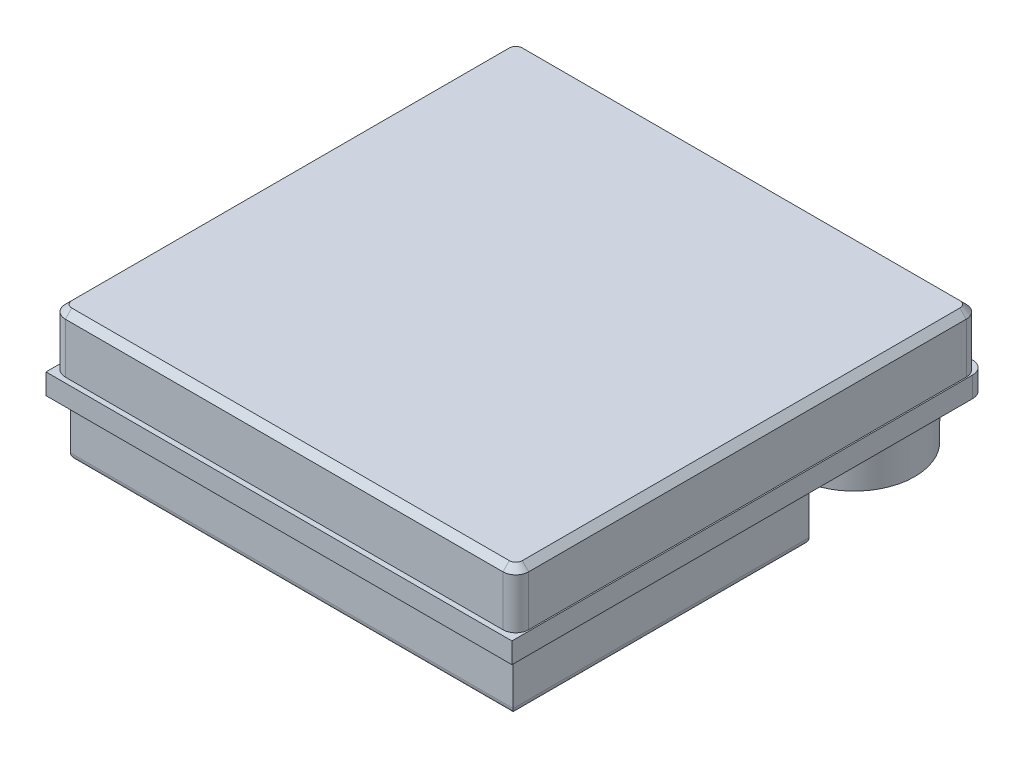
SolidWorks part; units mm, degrees
ref_plane "Front Plane" through (0, 0, 0) normal (0, 0, 1) x (1, 0, 0)
ref_plane "Top Plane" through (0, 0, 0) normal (0, 1, 0) x (1, 0, 0)
ref_plane "Right Plane" through (0, 0, 0) normal (1, 0, 0) x (0, 0, -1)
sketch "Sketch1" plane through (0, 0, 0) normal (0, 1, 0) x (1, 0, 0)
  line L1 (-9.05, 9.2) -> (9.05, 9.2)
  line L2 (-9.05, 9.2) -> (-9.05, -9.2)
  line L3 (-9.05, -9.2) -> (9.05, -9.2)
  line L4 (9.05, 9.2) -> (9.05, -9.2)
  line L5 (-9.05, 9.2) -> (9.05, -9.2) construction
  line L6 (-9.05, -9.2) -> (9.05, 9.2) construction
  point P0 (0, 0)
  dimension "D1" = 18.4
  dimension "D2" = 18.1
extrude "Boss-Extrude1" add sketch "Sketch1" along normal mid plane 0.8
sketch "Sketch2" plane through (0, 0.4, 0) normal (0, 1, 0) x (1, 0, 0)
  line L1 (9, 9) -> (-9, 9)
  line L2 (9, 9) -> (9, -9)
  line L3 (9, -9) -> (-9, -9)
  line L4 (-9, 9) -> (-9, -9)
  line L5 (9, 9) -> (-9, -9) construction
  line L6 (9, -9) -> (-9, 9) construction
  point P0 (0, 0)
  dimension "D1" = 18
extrude "Boss-Extrude2" add sketch "Sketch2" along normal blind 2.2
sketch "Sketch3" plane through (0, -0.4, 0) normal (0, -1, 0) x (1, 0, 0)
  line L0 (0, 9.2) -> (0, -9.2) construction
  line L1 (-9.05, 9.2) -> (9.05, 9.2) construction
  line L2 (9.05, -9.2) -> (-9.05, -9.2) construction
  line L4 (-3.075, -4.4) -> (3.075, -4.4)
  line L5 (-3.075, -4.4) -> (-3.075, -8.7)
  line L6 (-3.075, -8.7) -> (3.075, -8.7)
  line L7 (3.075, -4.4) -> (3.075, -8.7)
  line L8 (-3.075, -4.4) -> (3.075, -8.7) construction
  line L9 (-3.075, -8.7) -> (3.075, -4.4) construction
  point P6 (0, -6.55)
  dimension "D1" = 6.15
  dimension "D2" = 4.3
  dimension "D3" = 0.5
extrude "Boss-Extrude3" add sketch "Sketch3" along normal blind 3
sketch "Sketch4" plane through (0, 0, -8.7) normal (0, 0, -1) x (-1, 0, 0)
  line L8 (2.575, -0.9) -> (-2.575, -0.9)
  line L9 (-2.575, -0.9) -> (-2.575, -2.9)
  line L10 (-2.575, -2.9) -> (2.575, -2.9)
  line L11 (2.575, -2.9) -> (2.575, -0.9)
  line L12 (2.575, -0.9) -> (-2.575, -0.9)
  line L13 (-2.575, -0.9) -> (-2.575, -2.9)
  line L14 (-2.575, -2.9) -> (2.575, -2.9)
  line L15 (2.575, -2.9) -> (2.575, -0.9)
  dimension "D1" = 0.5
extrude "Cut-Extrude1" cut sketch "Sketch4" against normal blind 3.5
sketch "Sketch5" plane through (0, -0.4, 0) normal (0, -1, 0) x (1, 0, 0)
  line L0 (0, 9.2) -> (0, -9.2) construction
  line L1 (-9.05, 9.2) -> (9.05, 9.2) construction
  line L2 (9.05, -9.2) -> (-9.05, -9.2) construction
  line L4 (-8.6, 8.7) -> (8.6, 8.7)
  line L5 (-8.6, 8.7) -> (-8.6, -2.8)
  line L6 (-8.6, -2.8) -> (8.6, -2.8)
  line L7 (8.6, 8.7) -> (8.6, -2.8)
  line L8 (-8.6, 8.7) -> (8.6, -2.8) construction
  line L9 (-8.6, -2.8) -> (8.6, 8.7) construction
  point P6 (0, 2.95)
  dimension "D1" = 0.5
  dimension "D2" = 17.2
  dimension "D3" = 11.5
extrude "Boss-Extrude4" add sketch "Sketch5" along normal blind 2.2
fillet "Fillet1" radius 0.25 4 edges at (0, -2.6, -2.8) (-8.6, -2.6, 2.95) (0, -2.6, 8.7) (8.6, -2.6, 2.95)
sketch "Sketch6" plane through (0, -0.4, 0) normal (0, -1, 0) x (1, 0, 0)
  line L9 (8.85, -9) -> (8.85, 9)
  line L10 (8.85, 9) -> (-8.85, 9)
  line L11 (-8.85, 9) -> (-8.85, -9)
  line L12 (-8.85, -9) -> (8.85, -9)
  line L13 (8.85, -9) -> (8.85, 9)
  line L14 (8.85, 9) -> (-8.85, 9)
  line L15 (-8.85, 9) -> (-8.85, -9)
  line L16 (-8.85, -9) -> (8.85, -9)
  circle A0 centre (6.5, -6.65) radius 2.35
  dimension "D2" = 4.7
  dimension "D1" = 0.2
extrude "Boss-Extrude5" add sketch "Sketch6" along normal blind 1.7 contours A0
fillet "Fillet2" radius 0.5 4 edges at (-9, 1.5, -9) (-9, 1.5, 9) (9, 1.5, 9) (9, 1.5, -9)
chamfer "Chamfer1" distance 0.25 angle 45 8 edges at (9, 2.6, 0) (8.8536, 2.6, -8.8536) (8.8536, 2.6, 8.8536) (0, 2.6, -9) (0, 2.6, 9) (-8.8536, 2.6, -8.8536) (-8.8536, 2.6, 8.8536) (-9, 2.6, 0)
fillet "Fillet3" radius 0.5 2 edges at (-9.05, 0, -9.2) (9.05, 0, -9.2)
